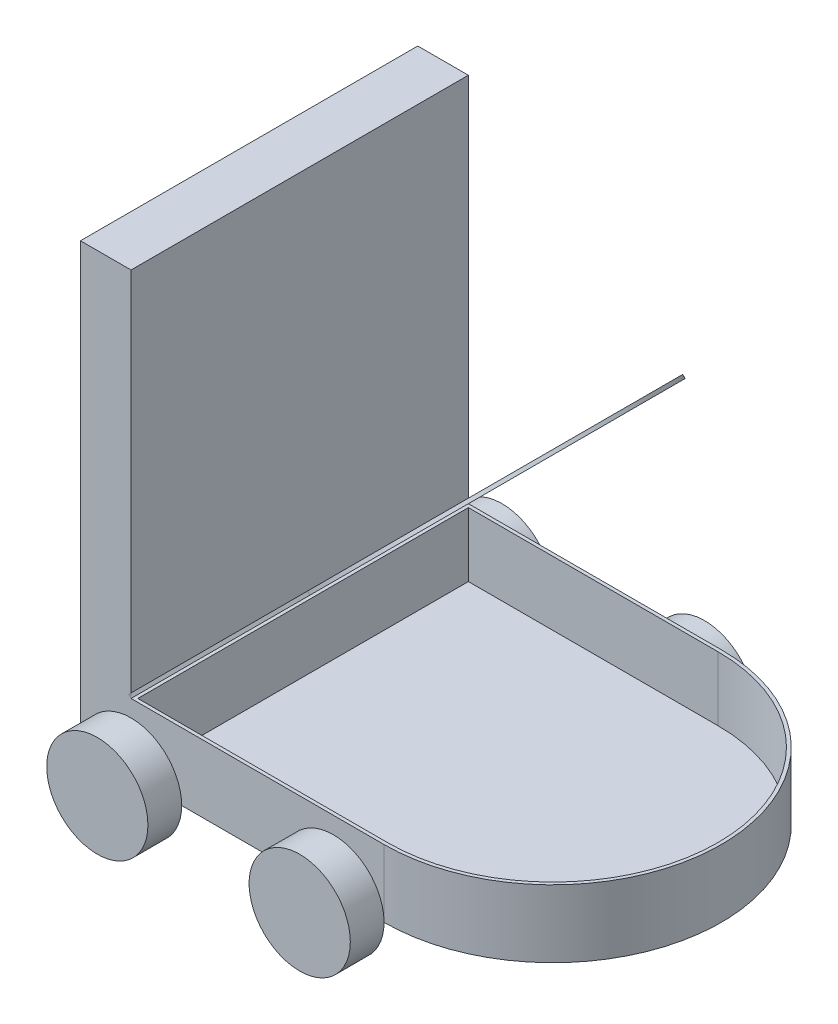
SolidWorks part; units mm, degrees
ref_plane "Front Plane" through (0, 0, 0) normal (0, 0, 1) x (1, 0, 0)
ref_plane "Top Plane" through (0, 0, 0) normal (0, 1, 0) x (1, 0, 0)
ref_plane "Right Plane" through (0, 0, 0) normal (1, 0, 0) x (0, 0, -1)
ref_plane "15mm Plane" through (0, 15, 0) normal (0, 1, 0) x (1, 0, 0)
sketch "Sketch1" plane through (0, 15, 0) normal (0, 1, 0) x (1, 0, 0)
  line L0 (15, 0) -> (15, 100)
  line L1 (15, 100) -> (90, 100)
  line L2 (15, 0) -> (90, 0)
  arc A0 (90, 100) -> (90, 0) centre (90, 50) cw
  dimension "D1" = 100
  dimension "D2" = 75
  dimension "D3" = 15
extrude "Horizontal body" add sketch "Sketch1" along normal blind 20
shell "Shell of base" thickness 1
sketch "Sketch3" plane through (0, 15, 0) normal (0, 1, 0) x (1, 0, 0)
  line L1 (0, 100) -> (15, 100)
  line L2 (0, 100) -> (0, 0)
  line L3 (0, 0) -> (15, 0)
  line L4 (15, 100) -> (15, 0)
  dimension "D1" = 15
extrude "Vertical body" add sketch "Sketch3" along normal blind 130
sketch "Sketch4" plane through (0, 0, 0) normal (0, 0, 1) x (1, 0, 0)
  line L0 (0, 15) -> (90, 15) construction
  line L2 (0, 145) -> (0, 15) construction
  circle A0 centre (15, 15) radius 15
  dimension "D1" = 30
  dimension "D2" = 15
extrude "Wheel" add sketch "Sketch4" along normal blind 10
pattern_linear "Wheel pattern" count 2 spacing 60 along (1, 0, 0) count 2 spacing 110 along (0, 0, -1) of "Wheel"
ref_plane "Lid plane" through (-10, 10, 0) normal (-0.7071, 0.7071, 0) x (0.7071, 0.7071, 0)
sketch "Sketch6" plane through (-10, 10, 0) normal (-0.7071, 0.7071, 0) x (0.7071, 0.7071, 0)
  line L2 (35.3553, 100) -> (35.3553, 0) construction
  line L3 (110.3553, 100) -> (35.3553, 100)
  line L4 (110.3553, 0) -> (35.3553, 0)
  line L5 (35.3553, 100) -> (35.3553, 0)
  line L6 (65.3553, 44.641) -> (45.3553, 10)
  line L7 (45.3553, 90) -> (85.3553, 90)
  line L8 (45.3553, 90) -> (45.3553, 50)
  line L9 (45.3553, 50) -> (85.3553, 50)
  line L10 (85.3553, 90) -> (85.3553, 50)
  line L11 (45.3553, 10) -> (85.3553, 10)
  line L12 (85.3553, 10) -> (65.3553, 44.641)
  line L14 (123.887, 25.7295) -> (141.5206, 50)
  line L15 (141.5206, 50) -> (123.887, 74.2705)
  line L16 (123.887, 74.2705) -> (95.3553, 65)
  line L17 (95.3553, 65) -> (95.3553, 35)
  line L18 (95.3553, 35) -> (123.887, 25.7295)
  arc A1 (110.3553, 100) -> (110.3553, 0) centre (110.3553, 50) cw
  circle A2 centre (116.0011, 50) radius 20.6457 construction
  dimension "D8" = 75
  dimension "D1" = 40
  dimension "D2" = 10
  dimension "D3" = 10
  dimension "D4" = 50
  dimension "D5" = 30
  dimension "D6" = 10
  dimension "D7" = 50
extrude "Lid" add sketch "Sketch6" along normal blind 1 separate body
